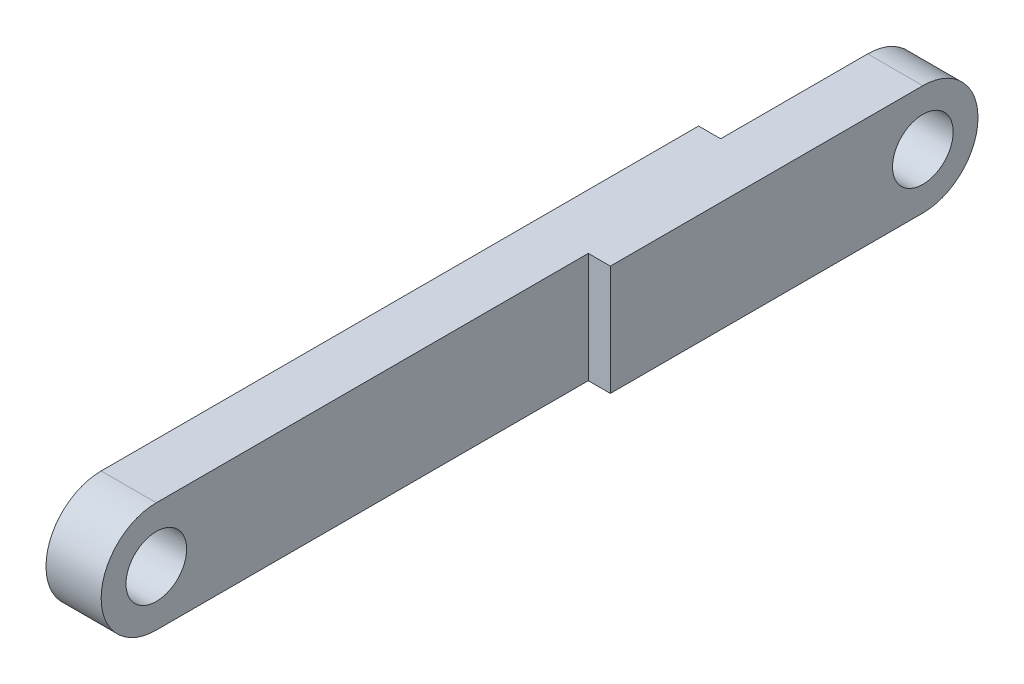
SolidWorks part; units mm, degrees
material "Plain Carbon Steel"
ref_plane "Front Plane" through (0, 0, 0) normal (0, 0, 1) x (1, 0, 0)
ref_plane "Top Plane" through (0, 0, 0) normal (0, 1, 0) x (1, 0, 0)
ref_plane "Right Plane" through (0, 0, 0) normal (1, 0, 0) x (0, 0, -1)
sketch "Sketch1" plane through (0, 0, 0) normal (1, 0, 0) x (0, 0, -1)
  line L24 (0, 3) -> (40.5, 3)
  line L25 (0, -3) -> (40.5, -3)
  arc A6 (0, 3) -> (0, -3) centre (0, 0) ccw
  arc A8 (40.5, 3) -> (40.5, -3) centre (40.5, 0) cw
  circle A10 centre (0, 0) radius 1.65
  circle A11 centre (40.5, 0) radius 1.65
  dimension "D1" = 6
  dimension "D2" = 40.5
  dimension "D3" = 3.3
extrude "Boss-Extrude1" add sketch "Sketch1" along normal blind 3
sketch "Sketch3" plane through (0, 0, 0) normal (-1, 0, 0) x (0, 0, 1)
  line L0 (-43.5, 3) -> (-32.5, 3)
  line L1 (-40.5, 3) -> (0, 3) construction
  line L2 (-32.5, 3) -> (-32.5, -3)
  line L3 (0, -3) -> (-40.5, -3) construction
  line L4 (-32.5, -3) -> (-43.5, -3)
  line L5 (-43.5, -3) -> (-43.5, 3)
  arc A1 (-40.5, 3) -> (-40.5, -3) centre (-40.5, 0) ccw construction
  dimension "D1" = 11
extrude "Cut-Extrude2" cut sketch "Sketch3" against normal blind 1.2
sketch "Sketch4" plane through (3, 0, 0) normal (1, 0, 0) x (0, 0, -1)
  line L0 (23.5, 3) -> (23.5, -3)
  line L5 (0, -3) -> (40.5, -3)
  line L6 (40.5, 3) -> (0, 3)
  line L7 (0, -3) -> (23.5, -3)
  line L8 (23.5, 3) -> (0, 3)
  arc A1 (40.5, -3) -> (40.5, 3) centre (40.5, 0) ccw construction
  arc A2 (0, 3) -> (0, -3) centre (0, 0) ccw
  arc A3 (40.5, -3) -> (40.5, 3) centre (40.5, 0) ccw
  arc A4 (0, 3) -> (0, -3) centre (0, 0) ccw
  circle M1 centre (40.5, 0) radius 1.65
  line M3 (0, -3) -> (40.5, -3)
  arc M4 (40.5, -3) -> (40.5, 3) centre (40.5, 0) ccw
  line M5 (40.5, 3) -> (0, 3)
  dimension "D2" = 17
  dimension "D1" = 0
extrude "Boss-Extrude2" add sketch "Sketch4" along normal blind 1.2 contours L0 M5 M3 M4 M1
